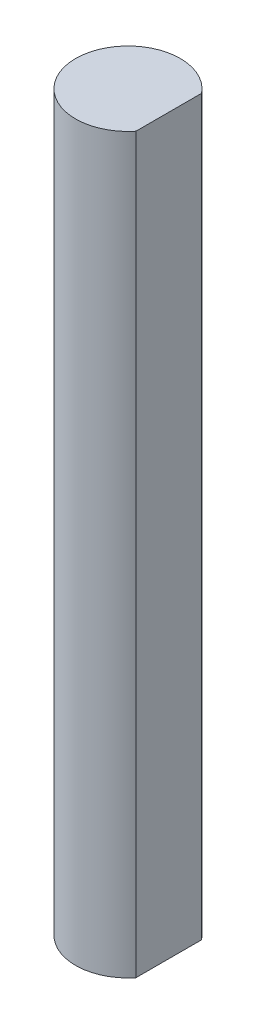
SolidWorks part; units mm, degrees
material "6061-T6 (SS)"
ref_plane "Front Plane" through (0, 0, 0) normal (0, 0, 1) x (1, 0, 0)
ref_plane "Top Plane" through (0, 0, 0) normal (0, 1, 0) x (1, 0, 0)
ref_plane "Right Plane" through (0, 0, 0) normal (1, 0, 0) x (0, 0, -1)
sketch "Sketch1" plane through (0, 0, 0) normal (0, 1, 0) x (1, 0, 0)
  line L0 (2.4721, 1.9923) -> (2.4721, -1.9923)
  arc A0 (2.4721, 1.9923) -> (2.4721, -1.9923) centre (0, 0) ccw
  dimension "D1" = 6.35
extrude "Boss-Extrude1" add sketch "Sketch1" along normal blind 63.5
sketch "Sketch3" plane through (0, 63.5, 0) normal (0, 1, 0) x (1, 0, 0)
  line L2 (2.4721, -1.9923) -> (2.4721, 1.9923)
  line L3 (2.4721, -1.9923) -> (2.4721, 1.9923)
  arc A2 (2.4721, 1.9923) -> (2.4721, -1.9923) centre (0, 0) ccw
  arc A3 (2.4721, 1.9923) -> (2.4721, -1.9923) centre (0, 0) ccw
  dimension "D1" = 0
extrude "Cut-Extrude1" cut sketch "Sketch3" against normal offset from surface (19.05 mm away) 44.45 up to face at (-0.3514, 0, 0)
